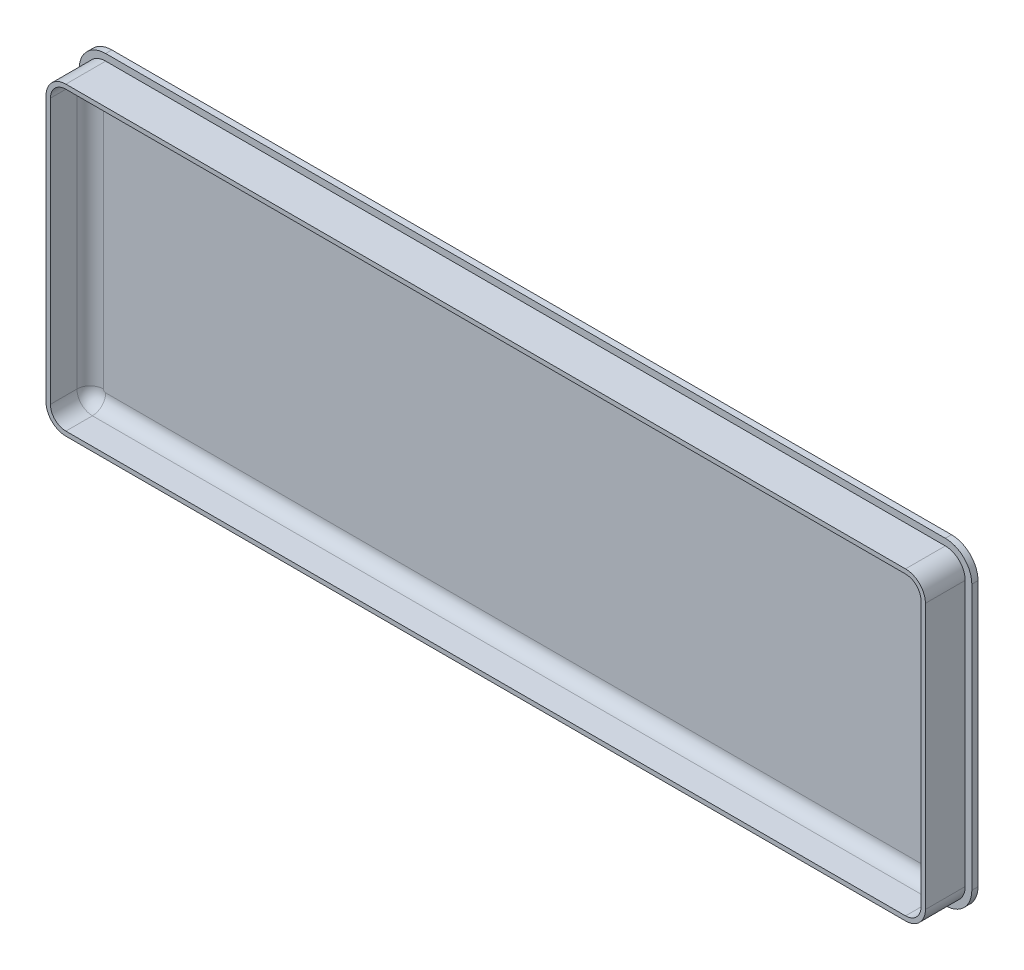
SolidWorks part; units mm, degrees
ref_plane "Front Plane" through (0, 0, 0) normal (0, 0, 1) x (1, 0, 0)
ref_plane "Top Plane" through (0, 0, 0) normal (0, 1, 0) x (1, 0, 0)
ref_plane "Right Plane" through (0, 0, 0) normal (1, 0, 0) x (0, 0, -1)
sketch "Sketch1" plane through (0, 0, 0) normal (0, 0, 1) x (1, 0, 0)
  line L1 (0, 0) -> (202, 0)
  line L2 (0, 0) -> (0, 72)
  line L3 (0, 72) -> (202, 72)
  line L4 (202, 0) -> (202, 72)
  dimension "D1" = 202
  dimension "D2" = 72
extrude "Boss-Extrude1" add sketch "Sketch1" along normal blind 1.4
sketch "Sketch2" plane through (0, 0, 1.4) normal (0, 0, 1) x (1, 0, 0)
  line L0 (0, 72) -> (0, 0) construction
  line L1 (1.5, 70.5) -> (200.5, 70.5)
  line L2 (1.5, 70.5) -> (1.5, 1.5)
  line L3 (1.5, 1.5) -> (200.5, 1.5)
  line L4 (200.5, 70.5) -> (200.5, 1.5)
  line L5 (2.5, 69.5) -> (199.5, 69.5)
  line L6 (2.5, 69.5) -> (2.5, 2.5)
  line L7 (2.5, 2.5) -> (199.5, 2.5)
  line L8 (199.5, 69.5) -> (199.5, 2.5)
  line L9 (202, 72) -> (0, 72) construction
  line L10 (0, 0) -> (202, 0) construction
  line L11 (202, 0) -> (202, 72) construction
  dimension "D1" = 1.5
  dimension "D2" = 1
  dimension "D3" = 1.5
  dimension "D4" = 1
  dimension "D5" = 1.5
  dimension "D6" = 1
  dimension "D7" = 1.5
  dimension "D8" = 1
extrude "Boss-Extrude2" add sketch "Sketch2" along normal blind 9
fillet "Fillet1" radius 3.5 4 edges at (2.5, 69.5, 5.9) (2.5, 2.5, 5.9) (199.5, 69.5, 5.9) (199.5, 2.5, 5.9)
fillet "Fillet2" radius 4.5 4 edges at (1.5, 70.5, 5.9) (1.5, 1.5, 5.9) (200.5, 70.5, 5.9) (200.5, 1.5, 5.9)
fillet "Fillet3" radius 6 4 edges at (202, 72, 0.7) (202, 0, 0.7) (0, 72, 0.7) (0, 0, 0.7)
fillet "Fillet4" radius 3 8 edges at (198.4749, 68.4749, 1.4) (199.5, 36, 1.4) (198.4749, 3.5251, 1.4) (101, 2.5, 1.4) (3.5251, 3.5251, 1.4) (2.5, 36, 1.4) (3.5251, 68.4749, 1.4) (101, 69.5, 1.4)
